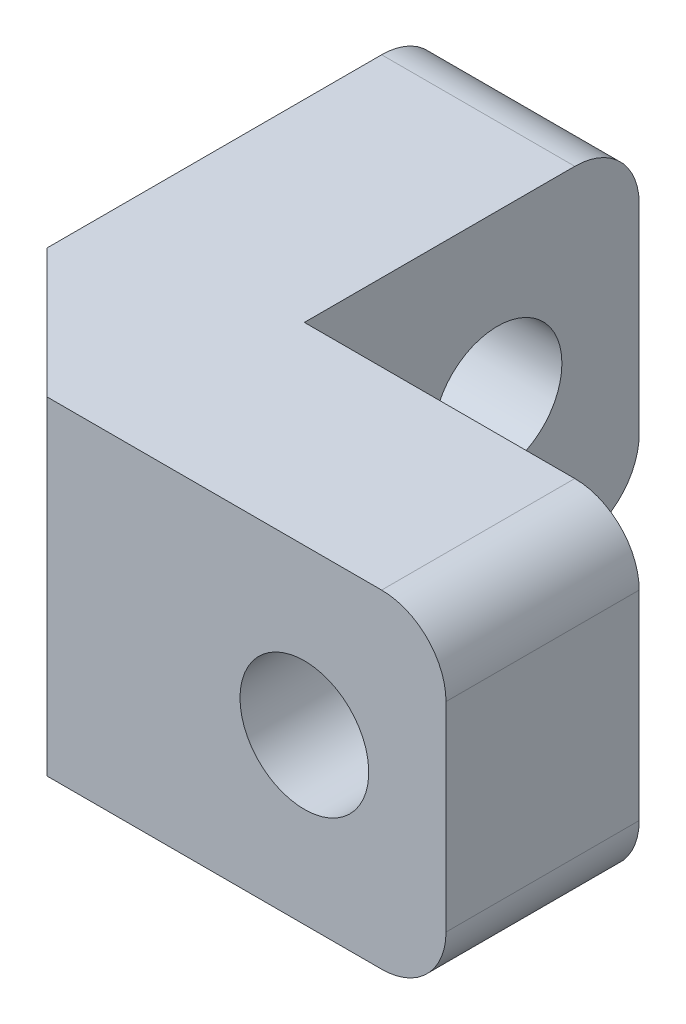
SolidWorks part; units mm, degrees
ref_plane "Front Plane" through (0, 0, 0) normal (0, 0, 1) x (1, 0, 0)
ref_plane "Top Plane" through (0, 0, 0) normal (0, 1, 0) x (1, 0, 0)
ref_plane "Right Plane" through (0, 0, 0) normal (1, 0, 0) x (0, 0, -1)
sketch "Sketch1" plane through (0, 0, 0) normal (0, 1, 0) x (1, 0, 0)
  line L0 (0, 0) -> (0, 5.2)
  line L1 (0, 5.2) -> (-3, 5.2)
  line L2 (-3, 5.2) -> (-3, -3)
  line L3 (-3, -3) -> (5.2, -3)
  line L4 (5.2, -3) -> (5.2, 0)
  line L5 (0, 0) -> (5.2, 0)
  dimension "D1" = 5.2
  dimension "D2" = 3
  dimension "D3" = 8.2
  dimension "D4" = 8.2
  dimension "D5" = 3
extrude "Boss-Extrude1" add sketch "Sketch1" along normal blind 5.1
chamfer "Chamfer1" distance 2 angle 45 1 edges at (-3, 2.55, 3)
fillet "Fillet1" radius 1 4 edges at (5.2, 0, 1.5) (5.2, 5.1, 1.5) (-1.5, 0, -5.2) (-1.5, 5.1, -5.2)
sketch "Sketch3" plane through (0, 0, 0) normal (1, 0, 0) x (0, 0, -1)
  line L1 (0, 5.1) -> (4.2, 5.1) construction
  line L2 (0, 5.1) -> (0, 0) construction
  circle A0 centre (3, 2.55) radius 1
  point P0 (3, 2.55)
  dimension "D3" = 2
  dimension "D1" = 3
  dimension "D2" = 2.55
extrude "Cut-Extrude1" cut sketch "Sketch3" against normal blind 5.1
sketch "Sketch4" plane through (0, 0, 0) normal (0, 0, -1) x (-1, 0, 0)
  line L0 (-4.2, 0) -> (0, 0) construction
  line L1 (0, 5.1) -> (0, 0) construction
  circle A0 centre (-3, 2.55) radius 1
  point P0 (-3, 2.55)
  dimension "D3" = 2
  dimension "D1" = 2.55
  dimension "D2" = 3
extrude "Cut-Extrude2" cut sketch "Sketch4" against normal blind 5.1
sketch "Sketch5" plane through (0, 0, 0) normal (0, 0, -1) x (-1, 0, 0)
  circle A0 centre (-3, 2.55) radius 1.7
  dimension "D1" = 3.4
extrude "Cut-Extrude3" cut sketch "Sketch5" against normal blind 1.4
sketch "Sketch6" plane through (-3, 0, 0) normal (-1, 0, 0) x (0, 0, 1)
  circle A0 centre (-3, 2.55) radius 1.7
  dimension "D1" = 3.4
extrude "Cut-Extrude4" cut sketch "Sketch6" against normal blind 1.4
